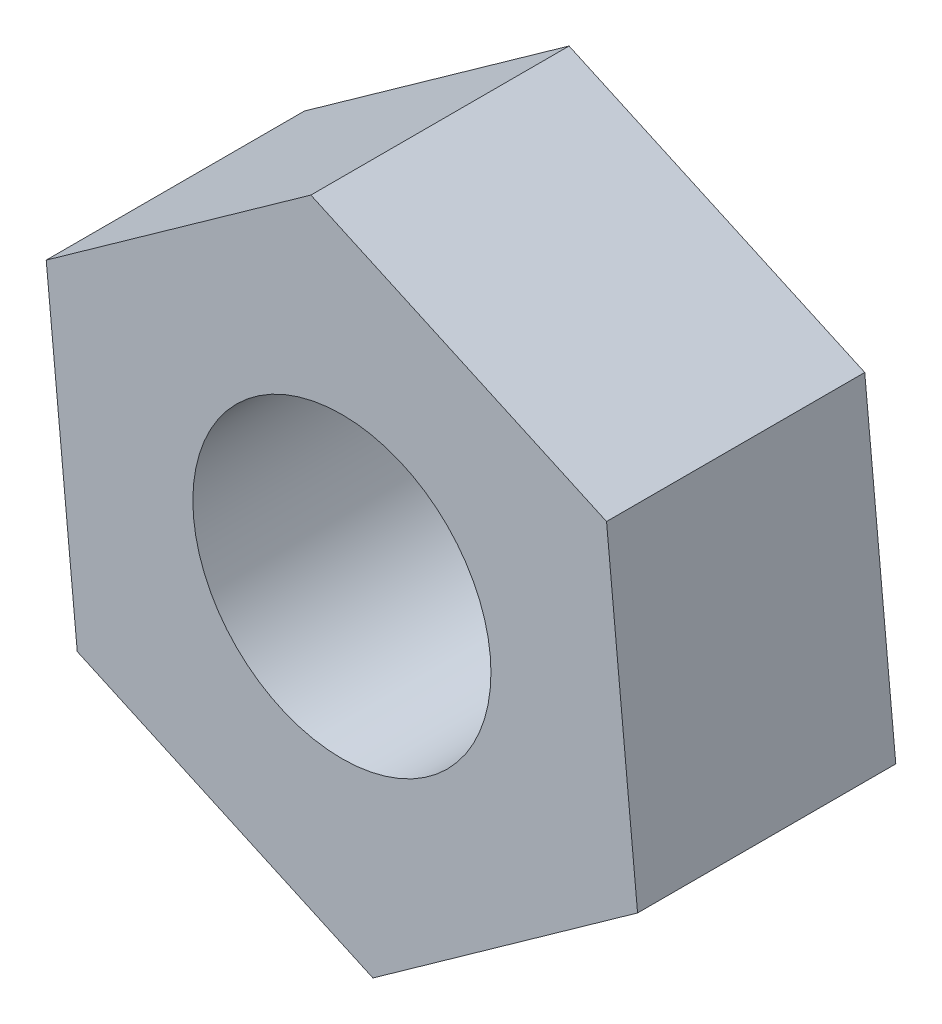
SolidWorks part; units mm, degrees
ref_plane "Front" through (0, 0, 0) normal (0, 0, 1) x (1, 0, 0)
ref_plane "Top" through (0, 0, 0) normal (0, 1, 0) x (1, 0, 0)
ref_plane "Right" through (0, 0, 0) normal (1, 0, 0) x (0, 0, -1)
sketch "Sketch1" plane through (0, 0, 0) normal (0, 0, 1) x (1, 0, 0)
  line L1 (-5.6371, -4.0179) -> (0.6611, -6.8908)
  line L2 (0.6611, -6.8908) -> (6.2981, -2.8729)
  line L3 (6.2981, -2.8729) -> (5.6371, 4.0179)
  line L4 (5.6371, 4.0179) -> (-0.6611, 6.8908)
  line L5 (-0.6611, 6.8908) -> (-6.2981, 2.8729)
  line L6 (-6.2981, 2.8729) -> (-5.6371, -4.0179)
  circle A0 centre (0, 0) radius 3.175
  circle A1 centre (0, 0) radius 5.995 construction
  dimension "D1" = 6.35
  dimension "D2" = 2.82
extrude "Boss-Extrude1" add sketch "Sketch1" along normal blind 5.5
